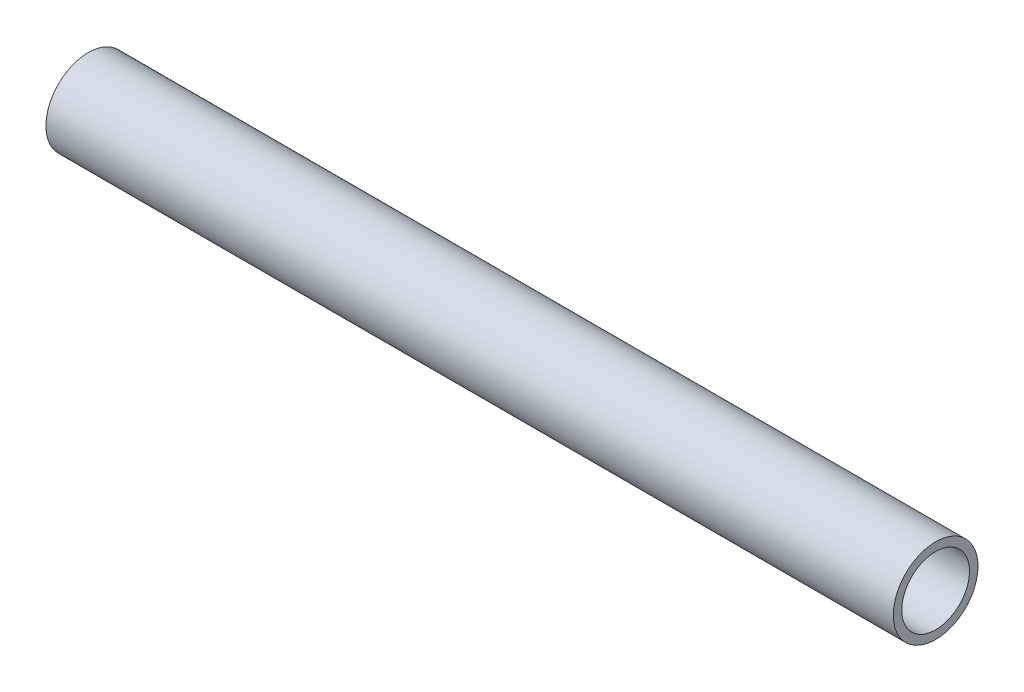
SolidWorks part; units mm, degrees
ref_plane "Front Plane" through (0, 0, 0) normal (0, 0, 1) x (1, 0, 0)
ref_plane "Top Plane" through (0, 0, 0) normal (0, 1, 0) x (1, 0, 0)
ref_plane "Right Plane" through (0, 0, 0) normal (1, 0, 0) x (0, 0, -1)
sketch "Sketch1" plane through (0, 0, 0) normal (0, 0, 1) x (1, 0, 0)
  line L0 (0, 0) -> (254, 0)
  dimension "D1" = 254
other "Tubing TUBING(1)"
ref_plane "Plane1" through (0, 0, 0) normal (1, 0, 0) x (0, 1, 0)
sketch "Sketch11" plane through (0, 0, 0) normal (1, 0, 0) x (0, 1, 0)
  circle A0 centre (0, 0) radius 12.7
  circle A1 centre (0, 0) radius 10.16
  point P5 (0, 12.7)
  point P6 (0, 10.16)
  point P7 (0, -12.7)
  point P8 (0, -10.16)
  point P9 (0, 0)
  dimension "D1" = 25.4
  dimension "D2" = 2.54
